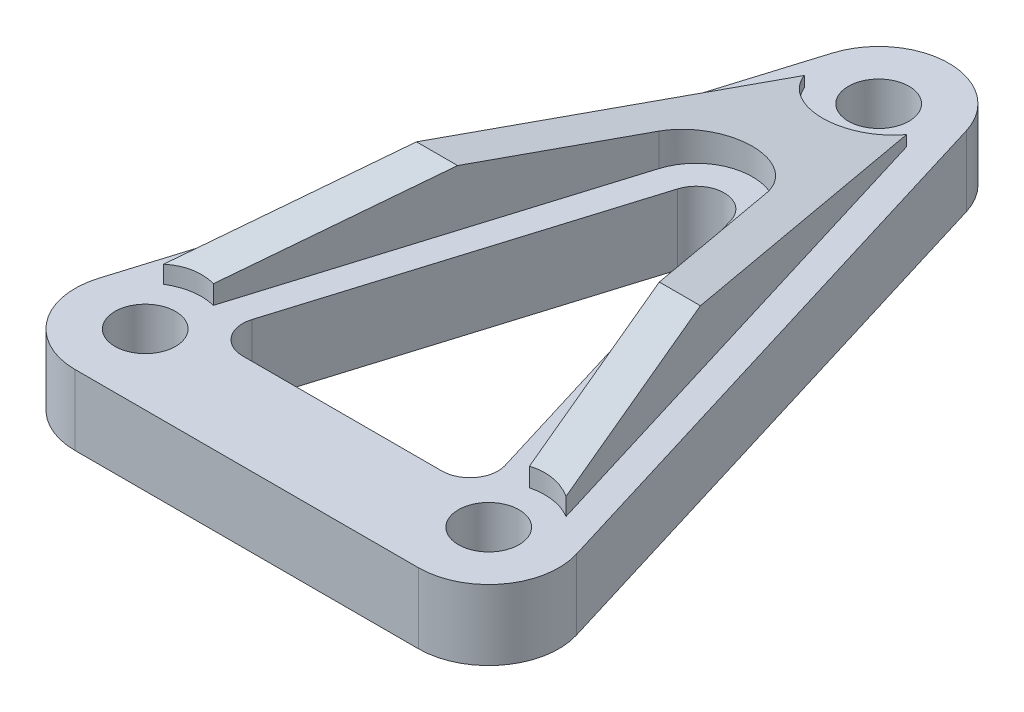
SolidWorks part; units mm, degrees
ref_plane "Front Plane" through (0, 0, 0) normal (0, 0, 1) x (1, 0, 0)
ref_plane "Top Plane" through (0, 0, 0) normal (0, 1, 0) x (1, 0, 0)
ref_plane "Right Plane" through (0, 0, 0) normal (1, 0, 0) x (0, 0, -1)
sketch "Sketch1" plane through (0, 0, 0) normal (0, 1, 0) x (1, 0, 0)
  line L0 (-3.0363, 0.9283) -> (-10.8018, -24.4717)
  line L1 (3.0363, 0.9283) -> (10.8018, -24.4717)
  line L2 (0, 0) -> (0, -15.171) construction
  line L3 (0, 0) -> (-7.7656, -25.4) construction
  line L4 (0, 0) -> (7.7656, -25.4) construction
  line L5 (7.7656, -28.575) -> (-7.7656, -28.575)
  line L6 (-1.2145, -7.8819) -> (-5.7191, -22.6157)
  line L7 (4.5046, -24.257) -> (-4.5046, -24.257)
  line L8 (1.2145, -7.8819) -> (5.7191, -22.6157)
  line L9 (6.2209, -24.257) -> (-6.2209, -24.257) construction
  line L10 (0, -3.9094) -> (6.2209, -24.257) construction
  line L11 (0, -3.9094) -> (-6.2209, -24.257) construction
  circle A0 centre (0, 0) radius 1.3716
  circle A1 centre (0, 0) radius 3.175 construction
  arc A2 (-3.0363, 0.9283) -> (3.0363, 0.9283) centre (0, 0) cw
  circle A3 centre (-7.7656, -25.4) radius 3.175 construction
  circle A4 centre (7.7656, -25.4) radius 3.175 construction
  circle A5 centre (-7.7656, -25.4) radius 1.3716
  circle A6 centre (7.7656, -25.4) radius 1.3716
  arc A7 (-10.8018, -24.4717) -> (-7.7656, -28.575) centre (-7.7656, -25.4) ccw
  arc A8 (10.8018, -24.4717) -> (7.7656, -28.575) centre (7.7656, -25.4) cw
  arc A9 (4.5046, -24.257) -> (5.7191, -22.6157) centre (4.5046, -22.987) ccw
  arc A10 (1.2145, -7.8819) -> (-1.2145, -7.8819) centre (0, -8.2532) ccw
  arc A11 (-5.7191, -22.6157) -> (-4.5046, -24.257) centre (-4.5046, -22.987) ccw
  arc A12 (0, -3.9094) -> (0, -3.9094) centre (0, -3.9094) cw construction
  arc A13 (6.2209, -24.257) -> (6.2209, -24.257) centre (6.2209, -24.257) cw construction
  arc A14 (-6.2209, -24.257) -> (-6.2209, -24.257) centre (-6.2209, -24.257) ccw construction
  dimension "D1" = 2.7432
  dimension "D2" = 6.35
  dimension "D5" = 25.4
  dimension "D7" = 4.318
  dimension "D8" = 2.7432
  dimension "D9" = 1.27
  dimension "D6" = 6.35
  dimension "D3" = 17
  dimension "D4" = 17
extrude "Body" add sketch "Sketch1" along normal mid plane 3.175
sketch "Sketch2" plane through (0, 1.5875, 0) normal (0, 1, 0) x (1, 0, 0)
  line L0 (-6.9336, -22.2444) -> (-8.4427, -27.1806)
  line L1 (6.9336, -22.2444) -> (8.4427, -27.1806)
  line L6 (-1.8218, 0.557) -> (-9.5873, -24.843)
  line L7 (-7.7656, -27.305) -> (7.7656, -27.305)
  line L8 (9.5873, -24.843) -> (1.8218, 0.557)
  line L9 (-1.8218, 0.557) -> (-9.5873, -24.843)
  line L10 (-7.7656, -27.305) -> (7.7656, -27.305)
  line L11 (9.5873, -24.843) -> (1.8218, 0.557)
  line L15 (-2.429, -7.5106) -> (-6.9336, -22.2444)
  line L16 (-4.5046, -25.527) -> (4.5046, -25.527)
  line L17 (6.9336, -22.2444) -> (2.429, -7.5106)
  line L18 (-2.429, -7.5106) -> (-6.9336, -22.2444)
  line L19 (-4.5046, -25.527) -> (4.5046, -25.527)
  line L20 (6.9336, -22.2444) -> (2.429, -7.5106)
  arc A6 (1.8218, 0.557) -> (-1.8218, 0.557) centre (0, 0) ccw
  arc A7 (-9.5873, -24.843) -> (-7.7656, -27.305) centre (-7.7656, -25.4) ccw
  arc A8 (7.7656, -27.305) -> (9.5873, -24.843) centre (7.7656, -25.4) ccw
  arc A9 (1.8218, 0.557) -> (-1.8218, 0.557) centre (0, 0) ccw
  arc A10 (-9.5873, -24.843) -> (-7.7656, -27.305) centre (-7.7656, -25.4) ccw
  arc A11 (7.7656, -27.305) -> (9.5873, -24.843) centre (7.7656, -25.4) ccw
  arc A15 (2.429, -7.5106) -> (-2.429, -7.5106) centre (0, -8.2532) ccw
  arc A16 (-6.9336, -22.2444) -> (-4.5046, -25.527) centre (-4.5046, -22.987) ccw
  arc A17 (4.5046, -25.527) -> (6.9336, -22.2444) centre (4.5046, -22.987) ccw
  arc A18 (2.429, -7.5106) -> (-2.429, -7.5106) centre (0, -8.2532) ccw
  arc A19 (-6.9336, -22.2444) -> (-4.5046, -25.527) centre (-4.5046, -22.987) ccw
  arc A20 (4.5046, -25.527) -> (6.9336, -22.2444) centre (4.5046, -22.987) ccw
  dimension "D1" = 1.27
  dimension "D2" = 1.27
extrude "Rib" add sketch "Sketch2" along normal blind 3.175
sketch "Sketch6" plane through (0, 0, 0) normal (1, 0, 0) x (0, 0, -1)
  line L0 (-14.4806, 4.1275) -> (2.0516, 1.5875)
  line L2 (3.175, 1.5875) -> (0.9283, 1.5875) construction
  line L3 (2.0516, 1.5875) -> (2.0516, 8.7897)
  line L4 (2.0516, 8.7897) -> (-27.1806, 8.7897)
  line L5 (-27.1806, 8.7897) -> (-27.1806, 1.5875)
  line L6 (-27.1806, 1.5875) -> (-14.4806, 4.1275)
  dimension "D1" = 2.54
  dimension "D2" = 12.7
extrude "Angle" cut sketch "Sketch6" against normal through all both and the other way through all
sketch "Sketch5" plane through (0, -1.5875, 0) normal (0, -1, 0) x (1, 0, 0)
  circle A0 centre (0, 0) radius 2.54
  circle A1 centre (7.7656, 25.4) radius 2.54
  circle A2 centre (-7.7656, 25.4) radius 2.54
  dimension "D1" = 5.08
extrude "Bolt hole" cut sketch "Sketch5" against normal blind 2.54 from vertex at -3.175 contours A0 | A1 | A2 starting at point (8.4427, 1.5875, 27.1806)
